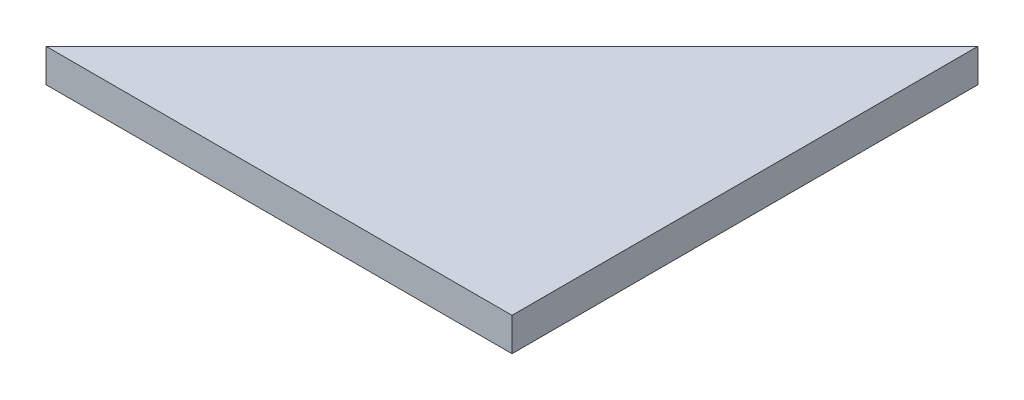
SolidWorks part; units mm, degrees
ref_plane "Front Plane" through (0, 0, 0) normal (0, 0, 1) x (1, 0, 0)
ref_plane "Top Plane" through (0, 0, 0) normal (0, 1, 0) x (1, 0, 0)
ref_plane "Right Plane" through (0, 0, 0) normal (1, 0, 0) x (0, 0, -1)
sketch "Sketch1" plane through (0, 0, 0) normal (0, 1, 0) x (1, 0, 0)
  line L0 (-21, -11.7149) -> (21, 30.2851)
  line L3 (-21, -11.7149) -> (21, -11.7149)
  line L4 (21, 30.2851) -> (21, -11.7149)
  point P0 (0, 0)
  dimension "D1" = 42
  dimension "D2" = 42
  dimension "D3" = 45
  dimension "D4" = 59.397
extrude "Boss-Extrude1" add sketch "Sketch1" along normal blind 3
